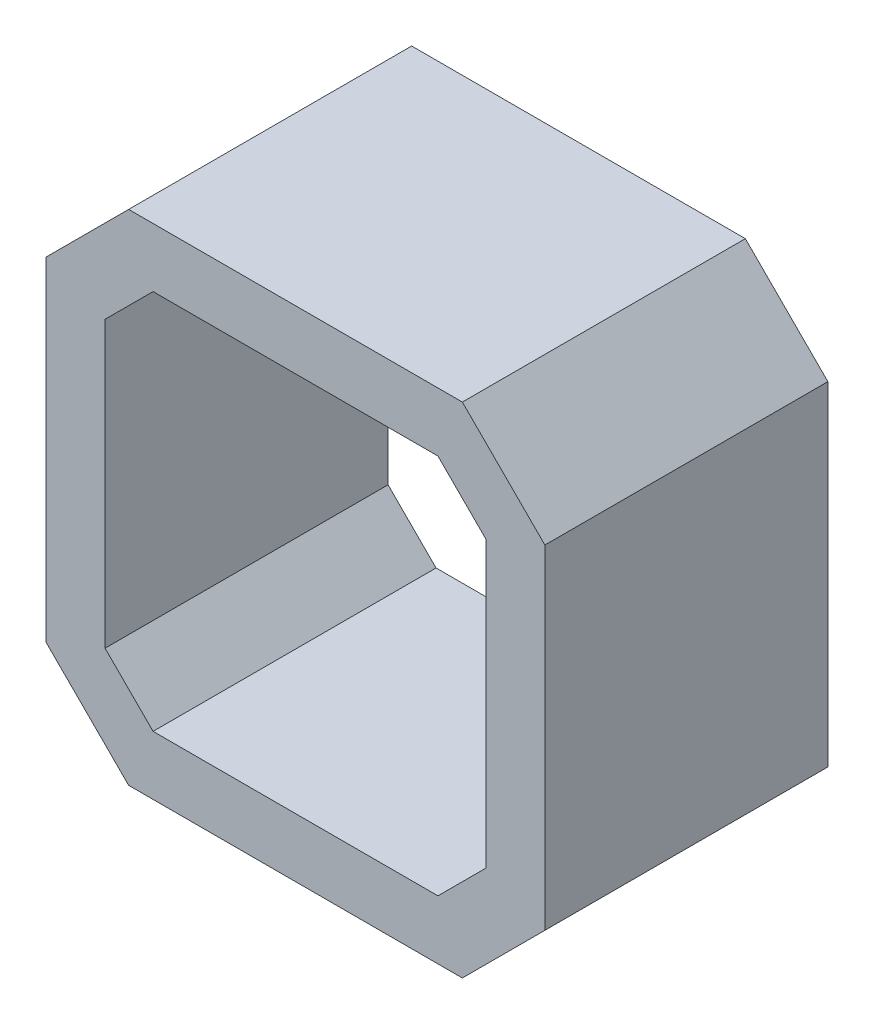
SolidWorks part; units mm, degrees
ref_plane "Ön Düzlem" through (0, 0, 0) normal (0, 0, 1) x (1, 0, 0)
ref_plane "Üst Düzlem" through (0, 0, 0) normal (0, 1, 0) x (1, 0, 0)
ref_plane "Sağ Düzlem" through (0, 0, 0) normal (1, 0, 0) x (0, 0, -1)
sketch "Çizim1" plane through (0, 0, 0) normal (0, 0, 1) x (1, 0, 0)
  line L0 (-21.15, 14.15) -> (-14.15, 21.15)
  line L1 (-14.15, 21.15) -> (14.15, 21.15)
  line L2 (-21.15, 14.15) -> (-21.15, -14.15)
  line L3 (-14.15, -21.15) -> (14.15, -21.15)
  line L4 (21.15, 14.15) -> (21.15, -14.15)
  line L5 (-21.15, 21.15) -> (21.15, -21.15) construction
  line L6 (-21.15, -21.15) -> (21.15, 21.15) construction
  line L7 (14.15, 21.15) -> (21.15, 14.15)
  line L8 (14.15, -21.15) -> (21.15, -14.15)
  line L9 (-21.15, -14.15) -> (-14.15, -21.15)
  line L10 (-12.0789, 16.15) -> (12.0789, 16.15)
  line L11 (12.0789, 16.15) -> (16.15, 12.0789)
  line L12 (16.15, 12.0789) -> (16.15, -12.0789)
  line L13 (12.0789, -16.15) -> (16.15, -12.0789)
  line L14 (-12.0789, -16.15) -> (12.0789, -16.15)
  line L15 (-16.15, -12.0789) -> (-12.0789, -16.15)
  line L16 (-16.15, 12.0789) -> (-16.15, -12.0789)
  line L17 (-16.15, 12.0789) -> (-12.0789, 16.15)
  point P0 (0, 0)
  dimension "D1" = 42.3
  dimension "D2" = 5
extrude "Yükseklik-Ekstrüzyon1" add sketch "Çizim1" along normal blind 24
